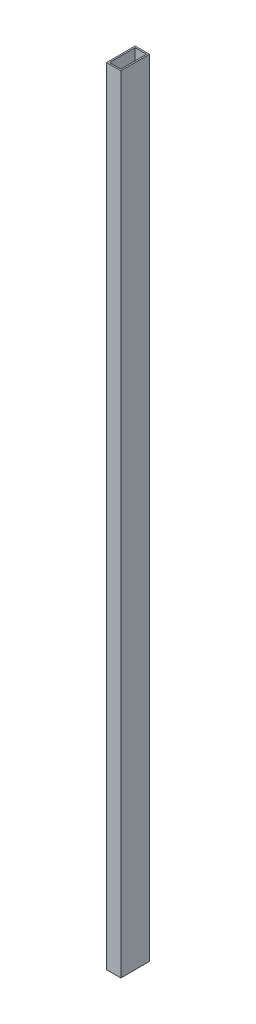
SolidWorks part; units mm, degrees
ref_plane "Спереди" through (0, 0, 0) normal (0, 0, 1) x (1, 0, 0)
ref_plane "Сверху" through (0, 0, 0) normal (0, 1, 0) x (1, 0, 0)
ref_plane "Справа" through (0, 0, 0) normal (1, 0, 0) x (0, 0, -1)
sketch "Эскиз1" plane through (0, 0, 0) normal (0, 1, 0) x (1, 0, 0)
  line L1 (-10, 20) -> (10, 20)
  line L2 (-10, 20) -> (-10, -20)
  line L3 (-10, -20) -> (10, -20)
  line L4 (10, 20) -> (10, -20)
  line L5 (-10, 20) -> (10, -20) construction
  line L6 (-10, -20) -> (10, 20) construction
  point P0 (0, 0)
extrude "Вытянуть-Тонкостенный1" add sketch "Эскиз1" along normal blind 1100 thin
